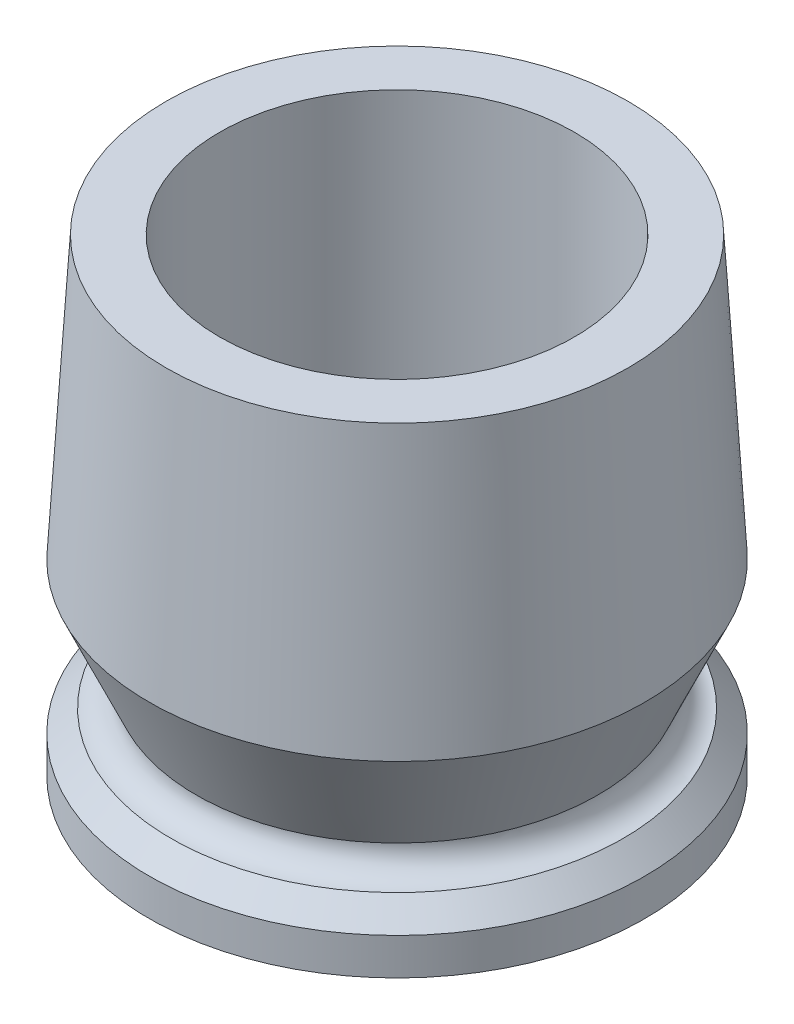
SolidWorks part; units mm, degrees
ref_plane "Front Plane" through (0, 0, 0) normal (0, 0, 1) x (1, 0, 0)
ref_plane "Top Plane" through (0, 0, 0) normal (0, 1, 0) x (1, 0, 0)
ref_plane "Right Plane" through (0, 0, 0) normal (1, 0, 0) x (0, 0, -1)
sketch "Sketch1" plane through (0, 0, 0) normal (0, 0, 1) x (1, 0, 0)
  line L0 (0, 0) -> (0, 70)
  line L1 (0, 70) -> (34.5, 70)
  line L2 (34.5, 70) -> (37, 28)
  line L3 (37, 28) -> (30, 12.5)
  line L4 (33.75, 8.75) -> (37, 5.5)
  line L5 (37, 5.5) -> (37, 0)
  line L6 (37, 0) -> (0, 0)
  line L7 (33.75, 8.75) -> (30, 12.5) construction
  line L9 (33.75, 8.75) -> (0, 8.75) construction
  arc A2 (30, 12.5) -> (33.75, 8.75) centre (33.75, 12.5) ccw
  point P12 (0, 0)
  dimension "D3" = 37
  dimension "D9" = 42
  dimension "D1" = 70
  dimension "D2" = 34.5
  dimension "D4" = 37
  dimension "D5" = 30
  dimension "D6" = 5.5
  dimension "D7" = 225
  dimension "D8" = 33.75
revolve "Revolve1" add sketch "Sketch1" angle 360 about L0
sketch "Sketch2" plane through (0, 70, 0) normal (0, 1, 0) x (1, 0, 0)
  circle A0 centre (0, 0) radius 26.5
  dimension "D1" = 53
extrude "Cut-Extrude1" cut sketch "Sketch2" against normal through all both
